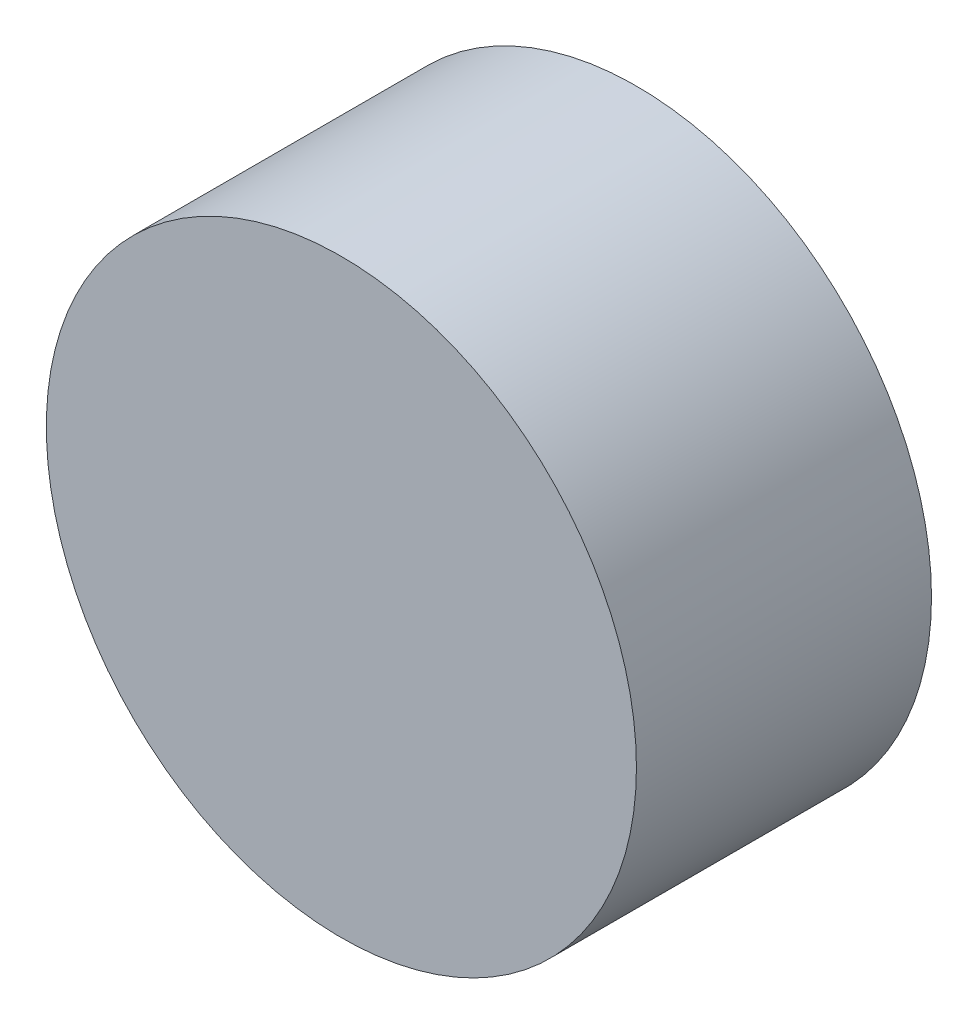
SolidWorks part; units mm, degrees
ref_plane "Front Plane" through (0, 0, 0) normal (0, 0, 1) x (1, 0, 0)
ref_plane "Top Plane" through (0, 0, 0) normal (0, 1, 0) x (1, 0, 0)
ref_plane "Right Plane" through (0, 0, 0) normal (1, 0, 0) x (0, 0, -1)
sketch "Sketch1" plane through (0, 0, 0) normal (0, 0, 1) x (1, 0, 0)
  circle A0 centre (0, 0) radius 6.35
  dimension "D1" = 12.7
extrude "Boss-Extrude1" add sketch "Sketch1" along normal blind 6.35
